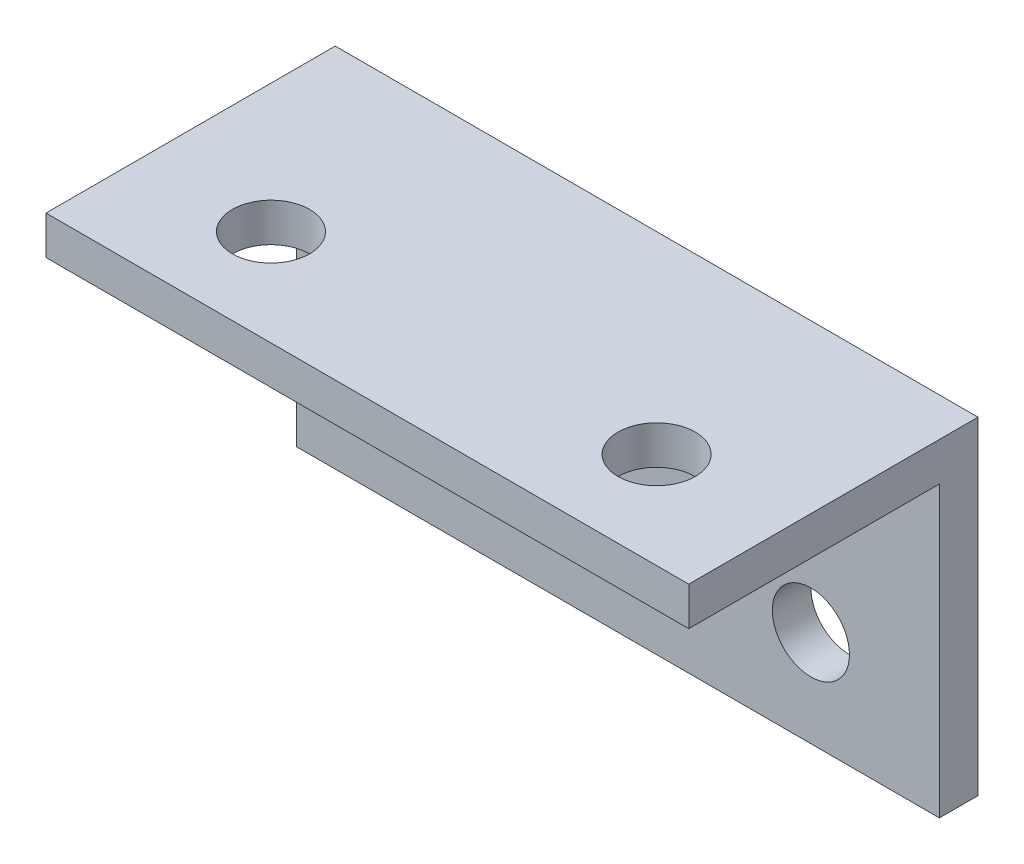
SolidWorks part; units mm, degrees
ref_plane "Front Plane" through (0, 0, 0) normal (0, 0, 1) x (1, 0, 0)
ref_plane "Top Plane" through (0, 0, 0) normal (0, 1, 0) x (1, 0, 0)
ref_plane "Right Plane" through (0, 0, 0) normal (1, 0, 0) x (0, 0, -1)
sketch "Sketch1" plane through (0, 0, 0) normal (0, 0, 1) x (1, 0, 0)
  line L0 (-17.8062, -2.0533) -> (-17.8062, -17.0533) construction
  line L1 (7.1938, -24.5533) -> (-42.8062, -24.5533)
  line L2 (7.1938, -24.5533) -> (7.1938, -2.0533)
  line L3 (7.1938, -2.0533) -> (-42.8062, -2.0533)
  line L4 (-42.8062, -24.5533) -> (-42.8062, -2.0533)
  line L5 (-17.8062, -17.0533) -> (-2.8062, -17.0533) construction
  circle A0 centre (-2.8062, -17.0533) radius 3
  circle A1 centre (-32.8062, -17.0533) radius 3
extrude "Boss-Extrude1" add sketch "Sketch1" along normal blind 3
sketch "Sketch3" plane through (0, -2.0533, 0) normal (0, 1, 0) x (1, 0, 0)
  line L0 (-42.8062, 0) -> (7.1938, 0)
  line L1 (7.1938, 0) -> (7.1938, -22.5)
  line L2 (7.1938, -22.5) -> (-42.8062, -22.5)
  line L3 (-42.8062, -22.5) -> (-42.8062, 0)
  line L4 (-17.8062, 0) -> (-17.8062, -15) construction
  line L5 (-17.8062, -15) -> (-2.8062, -15) construction
  circle A0 centre (-2.8062, -15) radius 3
  circle A1 centre (-32.8062, -15) radius 3
extrude "Boss-Extrude2" add sketch "Sketch3" along normal blind 3
